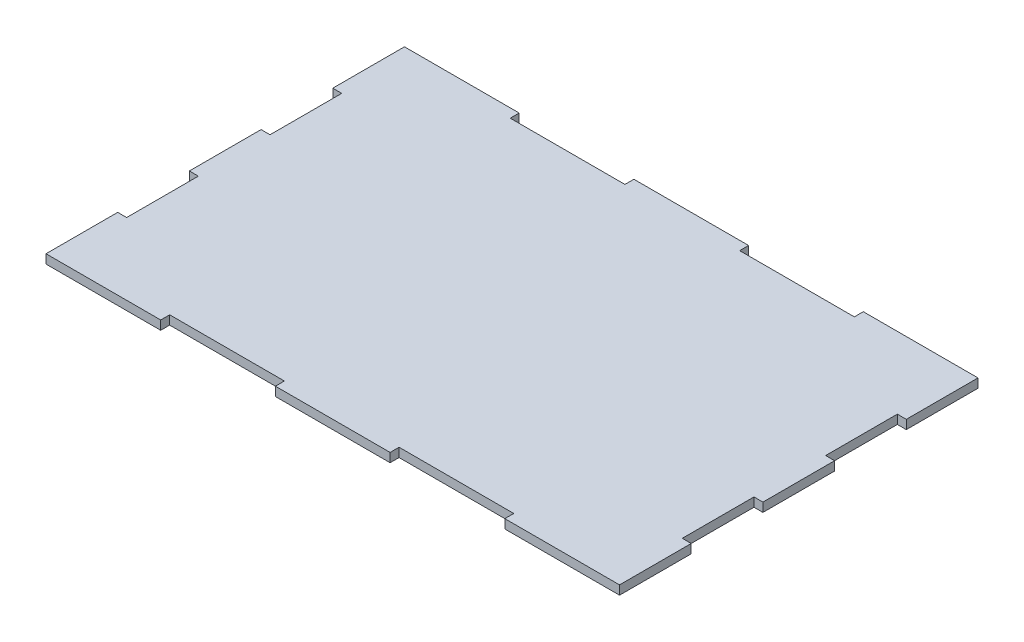
SolidWorks part; units mm, degrees
ref_plane "Front Plane" through (0, 0, 0) normal (0, 0, 1) x (1, 0, 0)
ref_plane "Top Plane" through (0, 0, 0) normal (0, 1, 0) x (1, 0, 0)
ref_plane "Right Plane" through (0, 0, 0) normal (1, 0, 0) x (0, 0, -1)
sketch "Sketch1" plane through (0, 0, 0) normal (0, 1, 0) x (1, 0, 0)
  line L1 (-101.6, -63.5) -> (101.6, -63.5)
  line L2 (-101.6, -63.5) -> (-101.6, 63.5)
  line L3 (-101.6, 63.5) -> (101.6, 63.5)
  line L4 (101.6, -63.5) -> (101.6, 63.5)
  line L5 (-101.6, -63.5) -> (101.6, 63.5) construction
  line L6 (-101.6, 63.5) -> (101.6, -63.5) construction
  point P0 (0, 0)
  dimension "D1" = 203.2
  dimension "D2" = 127
extrude "Boss-Extrude1" add sketch "Sketch1" along normal blind 3.175
ref_plane "Plane1" through (-101.6, 3.175, 63.5) normal (1, 0, 0) x (0, 0, -1)
sketch "Sketch3" plane through (0, 3.175, 0) normal (0, 1, 0) x (1, 0, 0)
  line L0 (-101.6, -63.5) -> (101.6, -63.5) construction
  line L1 (-20.32, -60.325) -> (-60.96, -60.325)
  line L2 (-20.32, -60.325) -> (-20.32, -63.5)
  line L3 (-20.32, -63.5) -> (-60.96, -63.5)
  line L4 (-60.96, -60.325) -> (-60.96, -63.5)
  line L5 (-101.6, -119.38) -> (-101.6, -7.62) construction
  dimension "D1" = 40.64
  dimension "D2" = 3.175
  dimension "D3" = 40.64
extrude "Cut-Extrude1" cut sketch "Sketch3" against normal blind 3.175
pattern_linear "LPattern1" count 2 spacing 81.28 along (1, 0, 0) of "Cut-Extrude1"
ref_plane "Plane7" through (-101.6, 3.175, -63.5) normal (-1, 0, 0) x (0, 0, 1)
sketch "Sketch5" plane through (0, 3.175, 0) normal (0, 1, 0) x (1, 0, 0)
  line L0 (101.6, 63.5) -> (-101.6, 63.5) construction
  line L1 (-20.32, 60.325) -> (-60.96, 60.325)
  line L2 (-20.32, 60.325) -> (-20.32, 63.5)
  line L3 (-20.32, 63.5) -> (-60.96, 63.5)
  line L4 (-60.96, 60.325) -> (-60.96, 63.5)
  line L5 (-101.6, 119.38) -> (-101.6, 7.62) construction
  dimension "D1" = 40.64
  dimension "D2" = 3.175
  dimension "D3" = 40.64
extrude "Cut-Extrude2" cut sketch "Sketch5" against normal blind 3.175
pattern_linear "LPattern2" count 2 spacing 81.28 along (1, 0, 0) of "Cut-Extrude2"
sketch "Sketch6" plane through (0, 3.175, 0) normal (0, 1, 0) x (1, 0, 0)
  line L0 (-101.6, -74.676) -> (-101.6, -52.324) construction
  line L1 (-101.6, -38.1) -> (-98.425, -38.1)
  line L2 (-101.6, -38.1) -> (-101.6, -12.7)
  line L3 (-101.6, -12.7) -> (-98.425, -12.7)
  line L4 (-98.425, -38.1) -> (-98.425, -12.7)
  line L5 (-60.96, -63.5) -> (-142.24, -63.5) construction
  point P9 (-101.6, -63.5)
  dimension "D1" = 3.175
  dimension "D2" = 25.4
  dimension "D3" = 25.4
extrude "Cut-Extrude3" cut sketch "Sketch6" against normal blind 3.175
pattern_linear "LPattern3" count 2 spacing 50.8 along (0, 0, -1) of "Cut-Extrude3"
sketch "Sketch7" plane through (0, 3.175, 0) normal (0, 1, 0) x (1, 0, 0)
  line L0 (101.6, -63.5) -> (101.6, 63.5) construction
  line L1 (101.6, -38.1) -> (98.425, -38.1)
  line L2 (101.6, -38.1) -> (101.6, -12.7)
  line L3 (101.6, -12.7) -> (98.425, -12.7)
  line L4 (98.425, -38.1) -> (98.425, -12.7)
  dimension "D1" = 25.4
  dimension "D2" = 3.175
  dimension "D3" = 25.4
extrude "Cut-Extrude4" cut sketch "Sketch7" against normal blind 3.175
pattern_linear "LPattern4" count 2 spacing 50.8 along (0, 0, -1) of "Cut-Extrude4"
